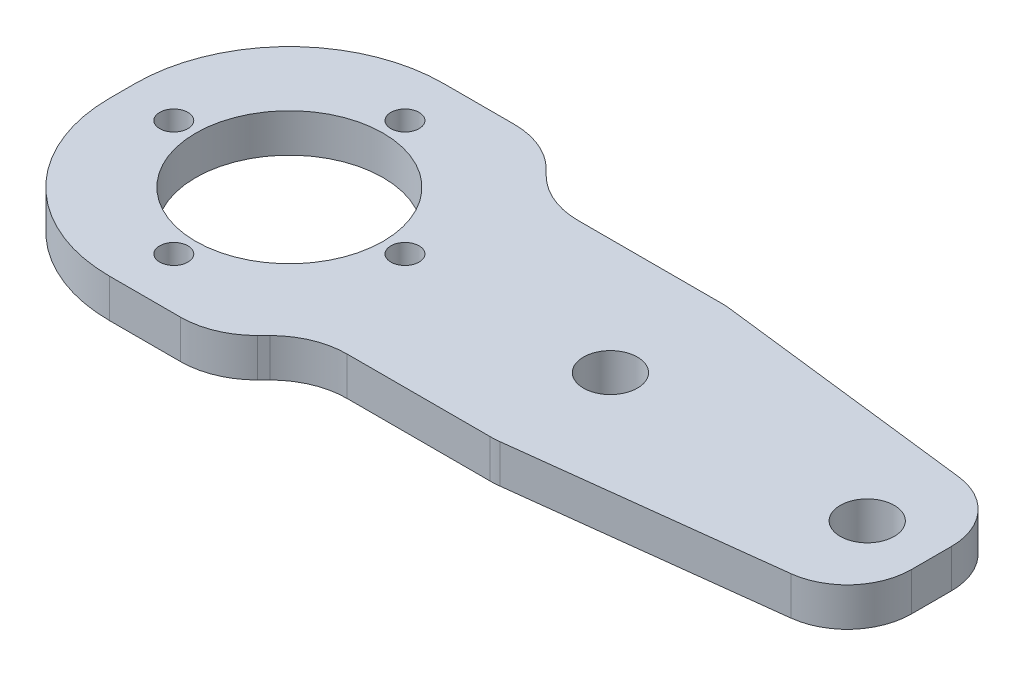
SolidWorks part; units mm, degrees
material "6061-T6 (SS)"
ref_plane "Front Plane" through (0, 0, 0) normal (0, 0, 1) x (1, 0, 0)
ref_plane "Top Plane" through (0, 0, 0) normal (0, 1, 0) x (1, 0, 0)
ref_plane "Right Plane" through (0, 0, 0) normal (1, 0, 0) x (0, 0, -1)
sketch "Sketch1" plane through (0, 0, 0) normal (0, 1, 0) x (1, 0, 0)
  line L0 (20, 26) -> (24, 22)
  line L2 (0, 0) -> (0, 26)
  line L5 (24, 22) -> (38, 22)
  line L6 (38, 22) -> (63, 19)
  line L7 (63, 19) -> (63, 7)
  line L11 (0, 26) -> (20, 26)
  line L12 (0, 0) -> (20, 0)
  line L13 (20, 0) -> (24, 4)
  line L14 (24, 4) -> (38, 4)
  line L15 (38, 4) -> (63, 7)
  circle A0 centre (13, 13) radius 7.3
  circle A2 centre (38, 13) radius 2.1
  circle A3 centre (58, 13) radius 2.1
  dimension "D4" = 14.6
  dimension "D9" = 25
  dimension "D11" = 14
  dimension "D12" = 4.2
  dimension "D13" = 4.2
  dimension "D1" = 26
  dimension "D2" = 4
  dimension "D3" = 13
  dimension "D5" = 4
  dimension "D6" = 4
  dimension "D7" = 20
  dimension "D8" = 0
  dimension "D10" = 14
  dimension "D14" = 6
  dimension "D15" = 13
  dimension "D16" = 0
  dimension "D17" = 6
  dimension "D18" = 5
  dimension "D19" = 5
  dimension "D20" = 20
  dimension "D21" = 20
  dimension "D22" = 4
extrude "Boss-Extrude1" add sketch "Sketch1" along normal blind 3
fillet "Fillet1" radius 12 2 edges at (0, 1.5, -26) (0, 1.5, 0)
fillet "Fillet4" radius 6 6 edges at (38, 1.5, -22) (38, 1.5, -4) (24, 1.5, -4) (24, 1.5, -22) (20, 1.5, -26) (20, 1.5, 0)
fillet "Fillet5" radius 5 2 edges at (63, 1.5, -7) (63, 1.5, -19)
sketch "Sketch2" plane through (0, 3, 0) normal (0, 1, 0) x (1, 0, 0)
  circle A0 centre (22, 13) radius 1.1
  circle A1 centre (13, 13) radius 7.3 construction
  circle A5 centre (13, 4) radius 1.1
  circle A6 centre (4, 13) radius 1.1
  circle A7 centre (13, 22) radius 1.1
  point P13 (13, 13)
  dimension "D2" = 2.2
  dimension "D1" = 9
  dimension "D4" = 0
  dimension "D3" = 4
extrude "Cut-Extrude1" cut sketch "Sketch2" against normal blind 10
